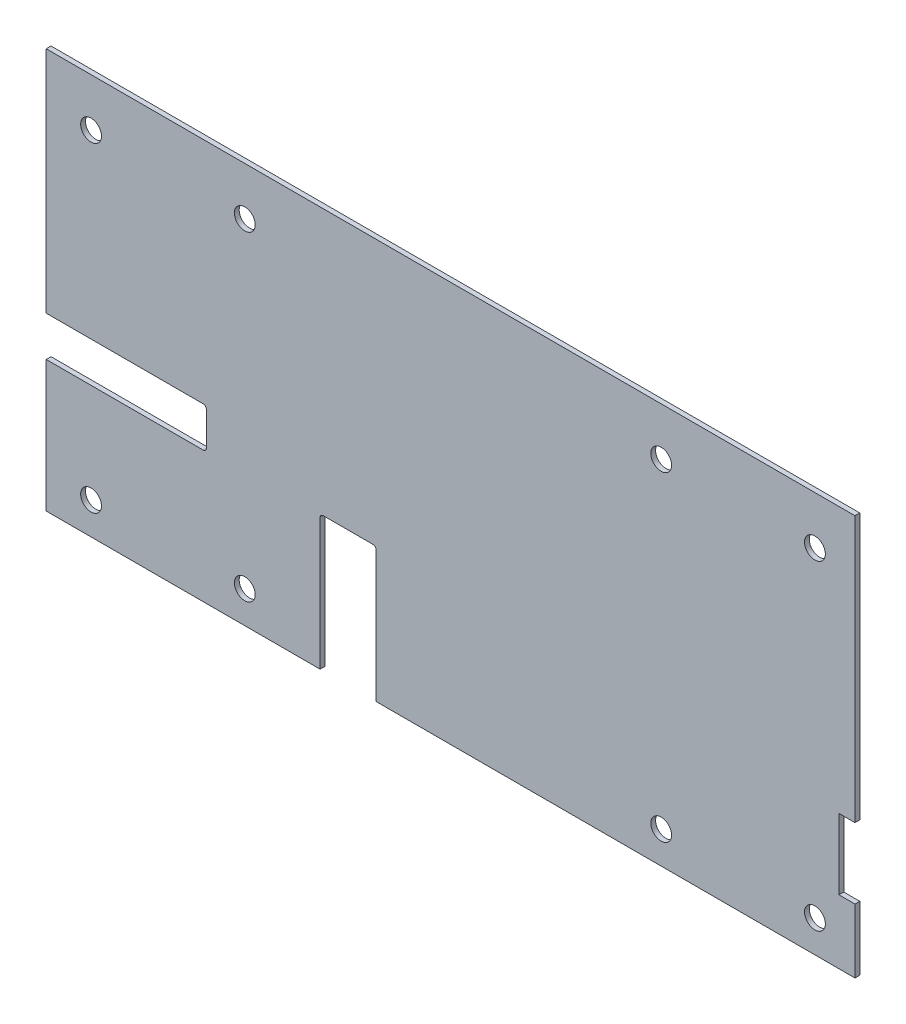
SolidWorks part; units mm, degrees
ref_plane "Plan de face" through (0, 0, 0) normal (0, 0, 1) x (1, 0, 0)
ref_plane "Plan de dessus" through (0, 0, 0) normal (0, 1, 0) x (1, 0, 0)
ref_plane "Plan de droite" through (0, 0, 0) normal (1, 0, 0) x (0, 0, -1)
sketch "Esquisse1" plane through (0, 0, 0) normal (0, 0, 1) x (1, 0, 0)
  line L1 (252.5, -125) -> (-252.5, -125)
  line L2 (252.5, -125) -> (252.5, 125)
  line L3 (252.5, 125) -> (-252.5, 125)
  line L4 (-252.5, -125) -> (-252.5, 125)
  line L5 (252.5, -125) -> (-252.5, 125) construction
  line L6 (252.5, 125) -> (-252.5, -125) construction
  line L7 (-224.5, 95) -> (-128.5, 95) construction
  line L8 (-224.5, 95) -> (-224.5, -105) construction
  line L9 (-224.5, -105) -> (-128.5, -105) construction
  line L10 (-128.5, 95) -> (-128.5, -105) construction
  line L11 (131.5, 95) -> (227.5, 95) construction
  line L12 (131.5, 95) -> (131.5, -105) construction
  line L13 (131.5, -105) -> (227.5, -105) construction
  line L14 (227.5, 95) -> (227.5, -105) construction
  circle A0 centre (131.5, 95) radius 6.5
  circle A1 centre (227.5, 95) radius 6.5
  circle A2 centre (131.5, -105) radius 6.5
  circle A3 centre (227.5, -105) radius 6.5
  circle A4 centre (-128.5, -105) radius 6.5
  circle A5 centre (-128.5, 95) radius 6.5
  circle A6 centre (-224.5, 95) radius 6.5
  circle A7 centre (-224.5, -105) radius 6.5
  point P0 (0, 0)
  dimension "D11" = 13
  dimension "D1" = 505
  dimension "D2" = 250
  dimension "D3" = 96
  dimension "D4" = 96
  dimension "D5" = 200
  dimension "D6" = 20
  dimension "D7" = 0
  dimension "D8" = 452
  dimension "D9" = 25
  dimension "D10" = 0
extrude "Boss.-Extru.1" add sketch "Esquisse1" along normal blind 3
sketch "Esquisse2" plane through (0, 0, 3) normal (0, 0, 1) x (1, 0, 0)
  line L0 (252.5, 125) -> (-252.5, 125) construction
  line L1 (-252.5, 125) -> (-152.5, 125)
  line L2 (-252.5, 125) -> (-252.5, 122)
  line L3 (-252.5, 122) -> (-152.5, 122)
  line L4 (-152.5, 125) -> (-152.5, 122)
  line L5 (-100, 125) -> (100, 125)
  line L6 (-100, 125) -> (-100, 122)
  line L7 (-100, 122) -> (100, 122)
  line L8 (100, 125) -> (100, 122)
  line L9 (252.5, -125) -> (252.5, 125) construction
  line L10 (252.5, 125) -> (152.545, 125)
  line L12 (249.5, 122) -> (152.545, 122)
  line L13 (152.545, 125) -> (152.545, 122)
  line L14 (252.5, -125) -> (249.5, -125)
  line L15 (252.5, -125) -> (252.5, -50)
  line L16 (252.5, -50) -> (249.5, -50)
  line L17 (249.5, -125) -> (249.5, -50)
  line L18 (252.5, 40) -> (249.5, 40)
  line L19 (252.5, 40) -> (252.5, 125)
  line L21 (249.5, 40) -> (249.5, 122)
  point P16 (0, 122)
  dimension "D1" = 100
  dimension "D2" = 100
  dimension "D3" = 3
  dimension "D4" = 0
  dimension "D5" = 200
  dimension "D6" = 3
  dimension "D7" = 75
  dimension "D8" = 85
extrude "Enlèv. mat.-Extru.1" [suppressed] cut sketch "Esquisse2" against normal blind 10
sketch "Esquisse3" [suppressed] plane through (0, 0, 3) normal (0, 0, 1) x (1, 0, 0)
  line L0 (274.5, 122) -> (274.5, 40) construction
  line L1 (-75.5, 122) -> (-72.5, 122)
  line L2 (-75.5, 122) -> (-75.5, 40)
  line L3 (-75.5, 40) -> (-72.5, 40)
  line L4 (-72.5, 122) -> (-72.5, 40)
  line L5 (-100, 122) -> (100, 122) construction
  line L7 (-277.5, -125) -> (274.5, -125) construction
  line L8 (-75.5, -125) -> (-72.5, -125)
  line L9 (-75.5, -125) -> (-75.5, -50)
  line L10 (-75.5, -50) -> (-72.5, -50)
  line L11 (-72.5, -125) -> (-72.5, -50)
  dimension "D1" = 3
  dimension "D2" = 350
  dimension "D3" = 0
  dimension "D4" = 82
  dimension "D5" = 75
  dimension "D6" = 0
extrude "Enlèv. mat.-Extru.2" [suppressed] cut sketch "Esquisse3" against normal blind 3
mirror "Symétrie1" [suppressed] about plane through (0, 0, 0) normal (1, 0, 0)
sketch "Esquisse4" plane through (0, 0, 3) normal (0, 0, 1) x (1, 0, 0)
  line L0 (-252.5, 125) -> (-252.5, -125) construction
  line L1 (-252.5, -43) -> (-152.5, -43)
  line L2 (-252.5, -43) -> (-252.5, -18)
  line L3 (-252.5, -18) -> (-152.5, -18)
  line L4 (-152.5, -43) -> (-152.5, -18)
  line L6 (-46.5, -41) -> (-81.5, -41)
  line L7 (-46.5, -41) -> (-46.5, -125)
  line L8 (-46.5, -125) -> (-81.5, -125)
  line L9 (-81.5, -41) -> (-81.5, -125)
  line L11 (-252.5, -125) -> (252.5, -125) construction
  line L12 (-252.5, 125) -> (-252.5, -125) construction
  line L13 (-250.1191, -43) -> (-253.0654, -43) construction
  line L14 (252.5, -125) -> (252.5, 125) construction
  line L15 (252.5, -41) -> (242.5, -41)
  line L16 (252.5, -41) -> (252.5, -85)
  line L17 (252.5, -85) -> (242.5, -85)
  line L18 (242.5, -41) -> (242.5, -85)
  dimension "D1" = 35
  dimension "D2" = 171
  dimension "D3" = 0
  dimension "D4" = 25
  dimension "D5" = 100
  dimension "D6" = 2
  dimension "D7" = 10
  dimension "D8" = 44
extrude "Enlèv. mat.-Extru.3" cut sketch "Esquisse4" against normal blind 10
sketch "Esquisse6" [suppressed] plane through (0, 0, 3) normal (0, 0, 1) x (1, 0, 0)
  line L1 (-274.5, -50) -> (-277.5, -50)
  line L2 (-274.5, -50) -> (-274.5, -45)
  line L3 (-274.5, -45) -> (-277.5, -45)
  line L4 (-277.5, -50) -> (-277.5, -45)
extrude "Enlèv. mat.-Extru.4" [suppressed] cut sketch "Esquisse6" against normal blind 10
fillet "Congé1" radius 2 4 edges at (-46.5, -41, 1.5) (-81.5, -41, 1.5) (-152.5, -43, 1.5) (-152.5, -18, 1.5)
